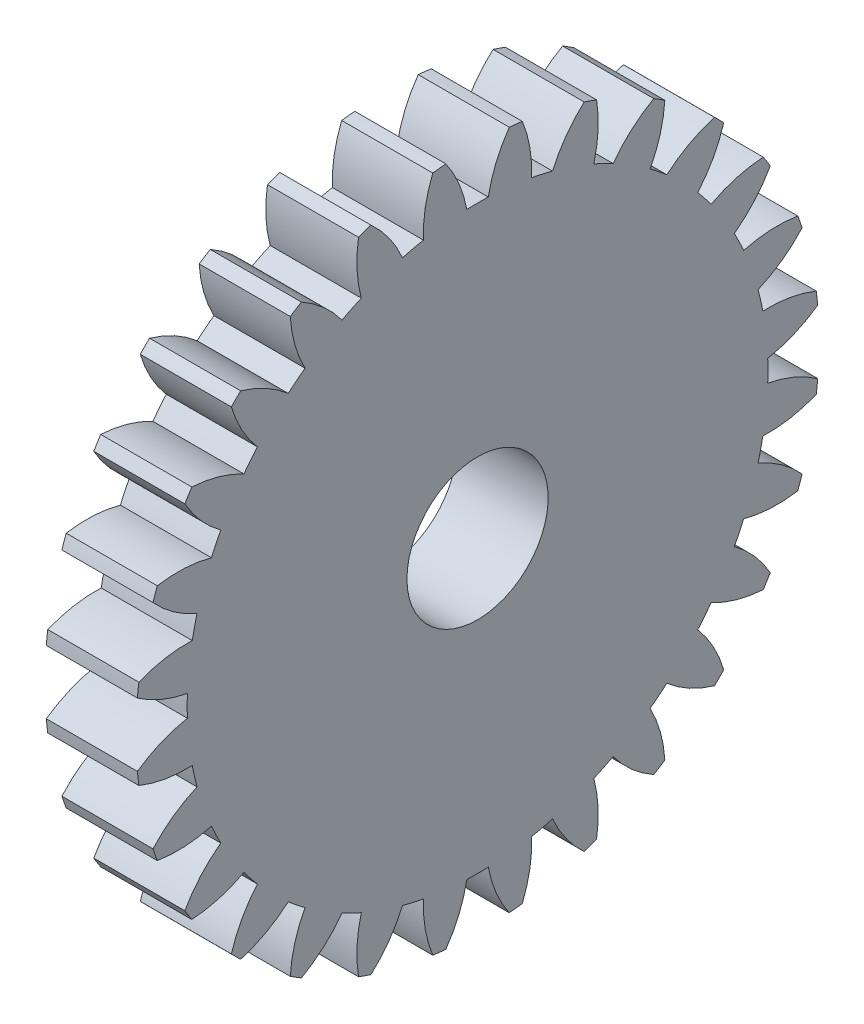
SolidWorks part; units mm, degrees
ref_plane "Plane1" through (0, 0, 0) normal (0, 0, 1) x (1, 0, 0)
ref_plane "Plane2" through (0, 0, 0) normal (0, 1, 0) x (1, 0, 0)
ref_plane "Plane3" through (0, 0, 0) normal (1, 0, 0) x (0, 0, -1)
sketch "HoldingSke" plane through (0, 0, 0) normal (0, 1, 0) x (1, 0, 0)
  line L0 (0, 0) -> (0.8829, -0.4695)
  line L1 (-15, 0) -> (100, 0) construction
  line L2 (0, 0) -> (-2.1039, 2.3779)
  line L3 (0, 0) -> (-11.863, 4.5341)
  line L4 (0, 0) -> (7.6251, 4.0544)
  line L5 (0, 0) -> (-46.8476, -17.4728)
  line L6 (0, 0) -> (-3.3159, -2.2372)
  line L7 (-2.1039, 2.3779) -> (8.6586, 51.2059)
  line L8 (-76.2, 54.61) -> (-75.2, 54.61)
  line L9 (-71.009, 38.7566) -> (-53.1078, 45.2721)
  line L10 (-76.2, 71.12) -> (104.1128, 71.12)
  line L11 (0, 0) -> (-4, 0)
  line L12 (-76.2, 101.6) -> (-76.162, 101.6)
  line L13 (24.9733, 27.94) -> (52.9518, 28.4284)
  line L14 (24.9733, 27.94) -> (24.9743, 27.94)
  line L15 (24.9733, 27.94) -> (100.4006, 29.5858)
  line L16 (-63.627, -1) -> (-12.827, -1)
  circle A0 centre (0, 0) radius 3
  circle A1 centre (0, 0) radius 12.749
  circle A2 centre (0, 0) radius 37.5
  circle A3 centre (0, 0) radius 3
  dimension "MHD" = 25.498
  dimension "Hub_dia" = 75
  dimension "Bore" = 6
  dimension "MBD" = 6
  dimension "Num_teeth" = 28
  dimension "Pitch" = 1
  dimension "Overall_len" = 50
  dimension "Show_teeth" = 28
  dimension "Thickness" = 4
  dimension "OAL" = 50.0001
  dimension "T_dim" = 1
  dimension "Ap" = 20
  dimension "H" = 19.05
  dimension "Pitch_radius" = 180.3128
  dimension "Width" = 4
  dimension "Backlash" = 0.038
  dimension "Addendum_fac" = 1
  dimension "Dedendum_fac" = 1.25
  dimension "Clearance_fac" = 0.25
  dimension "Dedendum_add" = 0.001
  dimension "Module" = 1
sketch "BasProSke" plane through (0, 0, 0) normal (0, 1, 0) x (1, 0, 0)
  line L0 (-10, 0) -> (60, 0) construction
  line L1 (0, 0) -> (0, 15)
  line L2 (0, 0) -> (4, 0)
  line L3 (4, 0) -> (4, 15)
  line L4 (4, 15) -> (0, 15)
  dimension "Thickness" = 4
  dimension "Diameter" = 30
revolve "Base-Revolve" add sketch "BasProSke" angle 360 about L0
sketch "TooCutSke" plane through (0, 0, 0) normal (1, 0, 0) x (0, 0, -1)
  line L1 (0, 0) -> (0, 107) construction
  line L2 (0, 0) -> (-0.8515, 13.9741) construction
  line L3 (0, 0) -> (-3.1309, 27.7873) construction
  line L4 (-0.8515, 13.9741) -> (-1.5654, 13.8936) construction
  arc A0 (0.4713, 12.7403) -> (-0.4713, 12.7403) centre (0, 0) ccw
  arc A1 (1.4098, 14.9591) -> (-1.4098, 14.9591) centre (0, 0) ccw
  circle A2 centre (0, 0) radius 14 construction
  circle A3 centre (0, 0) radius 13.1557 construction
  arc A4 (-0.4713, 12.7403) -> (-1.4098, 14.9591) centre (-5.9775, 11.7193) ccw
  arc A5 (1.4098, 14.9591) -> (0.4713, 12.7403) centre (5.9775, 11.7193) ccw
  dimension "Root_dia" = 25.498
  dimension "Overcut_dia" = 30.0508
  dimension "Pitch_dia" = 28
  dimension "Base_dia" = 26.3114
  dimension "Flank_rad" = 5.6
  dimension "Half_ang" = 6.429
  dimension "Half_CT" = 0.7185
extrude "ToothCut" cut sketch "TooCutSke" along normal through all
fillet "Breaks" [suppressed] radius 0.02
fillet "RootFillets" [suppressed] radius 0.251
pattern_circular "TeethCuts" count 28 every 12.857 about axis through (-10, 0, 0) along (1, 0, 0) of "ToothCut", "RootFillets", "Breaks"
sketch "HubNeaOneSke" plane through (0, 0, 0) normal (-1, 0, 0) x (0, 0, 1)
  circle A0 centre (0, 0) radius 12.749
  dimension "Diameter" = 25.498
extrude "HubNearOne" [suppressed] add sketch "HubNeaOneSke" along normal blind 46.0001
sketch "HubNeaBotSke" plane through (0, 0, 0) normal (-1, 0, 0) x (0, 0, 1)
  circle A0 centre (0, 0) radius 12.749
  dimension "Diameter" = 25.498
extrude "HubNearBoth" [suppressed] add sketch "HubNeaBotSke" along normal blind 23
ref_plane "FarPln" through (4, 0, 0) normal (1, 0, 0) x (0, 0, -1)
sketch "HubFarSke" plane through (4, 0, 0) normal (1, 0, 0) x (0, 0, -1)
  circle A0 centre (0, 0) radius 12.749
  dimension "Diameter" = 25.498
extrude "HubFar" [suppressed] add sketch "HubFarSke" along normal blind 23
sketch "BorSke" plane through (0, 0, 0) normal (1, 0, 0) x (0, 0, -1)
  circle A0 centre (0, 0) radius 3.1
  dimension "Diameter" = 6.2
extrude "Bore" cut sketch "BorSke" along normal mid plane 100.0001
sketch "KeySke" plane through (0, 0, 0) normal (1, 0, 0) x (0, 0, -1)
  line L0 (-1, 0) -> (-1, 4)
  line L1 (-1, 4) -> (1, 4)
  line L2 (1, 4) -> (1, 0)
  line L3 (0, 0) -> (0, 34) construction
  line L4 (-1, 0) -> (1, 0)
  dimension "Offset" = 4
  dimension "Width" = 2
extrude "Keyway" [suppressed] cut sketch "KeySke" along normal mid plane 100.0001
pattern_circular "Keyway2" [suppressed] count 2 every 90 about axis through (-10, 0, 0) along (1, 0, 0)
equation "' \"Module@HoldingSke\" = 6.35"
equation "' \"Num_teeth@HoldingSke\" = 12"
equation "' \"Ap@HoldingSke\" =  20"
equation "' \"Ap@HoldingSke\" = 20"
equation "' \"Width@HoldingSke\" = 0.5 * 25.4"
equation "' \"Hub_dia@HoldingSke\"= 1 * 25.4"
equation "' \"Hub_dia@HoldingSke\" = 1 * 25.4"
equation "' \"Overall_len@HoldingSke\" = 1.0 * 25.4"
equation "' \"Bore@HoldingSke\" = 0.75 * 25.4"
equation "' \"T_dim@HoldingSke\" = 0.1 * 25.4"
equation "' \"Width@KeySke\" = 0.25 * 25.4"
equation "' \"Show_teeth@HoldingSke\" = 13"
equation "' \"Backlash@HoldingSke\" = 0.009 * 25.4"
equation "' \"Addendum_fac@HoldingSke\" = 1.0"
equation "' \"Dedendum_fac@HoldingSke\" = 1.25"
equation "' \"Dedendum_add@HoldingSke\" = 0.00005 * 25.4"
equation "' \"Clearance_fac@HoldingSke\" = 0.25"
equation "\"Pitch@HoldingSke\" = 1 / \"Module@HoldingSke\""
equation "\"Overcut_dia@TooCutSke\" = (\"Num_teeth@HoldingSke\" + 2 * \"Addendum_fac@HoldingSke\") / \"Pitch@HoldingSke\" + 0.002 * 25.4"
equation "\"Pitch_dia@TooCutSke\" = \"Num_teeth@HoldingSke\" / \"Pitch@HoldingSke\""
equation "\"Base_dia@TooCutSke\" = \"Num_teeth@HoldingSke\" / \"Pitch@HoldingSke\" * cos((\"Ap@HoldingSke\"  * 3.14159265 / 180))"
equation "\"Root_dia@TooCutSke\" = (\"Num_teeth@HoldingSke\" + 2) / \"Pitch@HoldingSke\" - 2 * (\"Addendum_fac@HoldingSke\" + \"Dedendum_fac@HoldingSke\") / \"Pitch@HoldingSke\" - \"Dedendum_add@HoldingSke\" * 2"
equation "\"Half_ang@TooCutSke\" = 180 / \"Num_teeth@HoldingSke\""
equation "\"Half_CT@TooCutSke\" = \"Num_teeth@HoldingSke\" / \"Pitch@HoldingSke\" * sin((3.14159265 / 2 / \"Num_teeth@HoldingSke\")) / 2 - 7 * \"Backlash@HoldingSke\" / 4"
equation "\"Flank_rad@TooCutSke\" = \"Num_teeth@HoldingSke\" / \"Pitch@HoldingSke\" / 5"
equation "\"Radius@RootFillets\" = \"Clearance_fac@HoldingSke\" / \"Pitch@HoldingSke\" + \"Dedendum_add@HoldingSke\""
equation "\"Break_rad@Breaks\" = 0.02 / \"Pitch@HoldingSke\""
equation "\"Thickness@HoldingSke\" = \"Width@HoldingSke\""
equation "\"OAL@HoldingSke\" = \"Thickness@HoldingSke\""
equation "\"MHD@HoldingSke\" = (\"Num_teeth@HoldingSke\" + 2) / \"Pitch@HoldingSke\" - 2 * (\"Addendum_fac@HoldingSke\" + \"Dedendum_fac@HoldingSke\")  / \"Pitch@HoldingSke\" - \"Dedendum_add@HoldingSke\" * 2"
equation "\"MBD@HoldingSke\" = (\"Num_teeth@HoldingSke\" + 2) / \"Pitch@HoldingSke\" - 2 * (\"Addendum_fac@HoldingSke\" + \"Dedendum_fac@HoldingSke\")  / \"Pitch@HoldingSke\" - \"Dedendum_add@HoldingSke\" * 2 - 0.002 * 25.4"
equation "\"MHD@HoldingSke\" = ((sgn( \"MHD@HoldingSke\" - \"Hub_dia@HoldingSke\" )-1)*( \"MHD@HoldingSke\" - \"Hub_dia@HoldingSke\" ))/-2+ \"Hub_dia@HoldingSke\""
equation "\"MBD@HoldingSke\" = ((sgn( \"MBD@HoldingSke\" - \"Bore@HoldingSke\" )-1)*( \"MBD@HoldingSke\" - \"Bore@HoldingSke\" ))/-2+ \"Bore@HoldingSke\""
equation "\"OAL@HoldingSke\" = ((sgn( \"OAL@HoldingSke\" - \"Overall_len@HoldingSke\" )+1)*( \"OAL@HoldingSke\" - \"Overall_len@HoldingSke\" ))/2 + \"Overall_len@HoldingSke\" + 0.000002 * 25.4"
equation "\"Num_teeth@TeethCuts\" = int( \"Show_teeth@HoldingSke\" ) + 1"
equation "\"Num_teeth@TeethCuts\" = ((sgn( \"Num_teeth@TeethCuts\" - \"Num_teeth@HoldingSke\" )-1)*( \"Num_teeth@TeethCuts\" - \"Num_teeth@HoldingSke\" ))/-2+ \"Num_teeth@HoldingSke\""
equation "\"Num_teeth@TeethCuts\" = ((sgn( \"Num_teeth@TeethCuts\" - 2.0)+1)*( \"Num_teeth@TeethCuts\" - 2.0))/2 +2.0"
equation "\"Angle@TeethCuts\" = 360.0 / \"Num_teeth@HoldingSke\""
equation "\"Diameter@BasProSke\" = (\"Num_teeth@HoldingSke\" + 2 * \"Addendum_fac@HoldingSke\") / \"Pitch@HoldingSke\""
equation "\"Thickness@BasProSke\"  = \"Thickness@HoldingSke\""
equation "' \"Fillet_rad@BasProSke\" =  \"Thickness@HoldingSke\" * 0.05"
equation "' \"Fillet_rad@BasProSke\" = \"Thickness@HoldingSke\" * 0.05"
equation "\"MHD@HoldingSke\" = ((sgn( \"MHD@HoldingSke\" - \"Root_dia@TooCutSke\" )-1)*( \"MHD@HoldingSke\" - \"Root_dia@TooCutSke\" ))/-2+ \"Root_dia@TooCutSke\""
equation "\"Diameter@HubNeaOneSke\" = \"MHD@HoldingSke\""
equation "\"Length@HubNearOne\" = \"OAL@HoldingSke\" - \"Thickness@BasProSke\""
equation "\"Diameter@HubNeaBotSke\" = \"MHD@HoldingSke\""
equation "\"Length@HubNearBoth\" = ( \"OAL@HoldingSke\" - \"Thickness@BasProSke\" ) / 2.0"
equation "\"Thickness@FarPln\" = \"Thickness@BasProSke\""
equation "\"Diameter@HubFarSke\" = \"MHD@HoldingSke\""
equation "\"Length@HubFar\" = ( \"OAL@HoldingSke\" - \"Thickness@BasProSke\" ) / 2.0"
equation "\"D1@Bore\" = \"OAL@HoldingSke\" * 2.0"
equation "\"D1@Keyway\" = \"OAL@HoldingSke\" * 2.0"
equation "\"Offset@KeySke\" = \"T_dim@HoldingSke\" + \"MBD@HoldingSke\" / 2.0"
